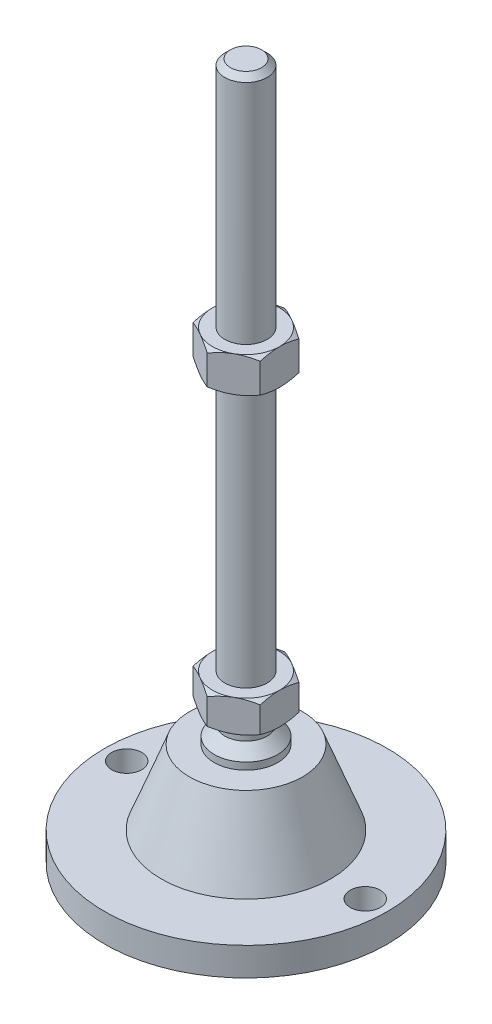
SolidWorks part; units mm, degrees
ref_plane "Спереди" through (0, 0, 0) normal (0, 0, 1) x (1, 0, 0)
ref_plane "Сверху" through (0, 0, 0) normal (0, 1, 0) x (1, 0, 0)
ref_plane "Справа" through (0, 0, 0) normal (1, 0, 0) x (0, 0, -1)
sketch "Эскиз1" plane through (0, 0, 0) normal (0, 0, 1) x (1, 0, 0)
  line L0 (0, 0) -> (-40, 0)
  line L3 (-40, 0) -> (-40, 8)
  line L12 (-6, 47) -> (-6, 195.4)
  line L13 (-6, 195.4) -> (-4.4, 197)
  line L14 (-4.4, 197) -> (0, 197)
  line L15 (0, 197) -> (0, 0) construction
  line L16 (-40, 8) -> (-24, 8)
  line L17 (0, 0) -> (0, 197)
  line L18 (0, 0) -> (0, -7.9595) construction
  line L19 (-6, 47) -> (-6, 38)
  line L21 (-9, 29) -> (-16, 29)
  line L22 (-24, 8) -> (-16, 29)
  line L23 (-9, 29) -> (-9, 31)
  line L24 (-9, 31) -> (-6, 34)
  line L25 (-6, 34) -> (-6, 38)
  line L26 (-6, 47) -> (0, 47) construction
  point P8 (-6, 121.2)
revolve "Повернуть1" add sketch "Эскиз1" angle 360 about L17
ref_plane "Плоскость2" through (0, 38, 0) normal (0, 1, 0) x (1, 0, 0)
sketch "Эскиз2" plane through (0, 38, 0) normal (0, 1, 0) x (1, 0, 0)
  line L1 (0, 10.9697) -> (-9.5, 5.4848)
  line L2 (-9.5, 5.4848) -> (-9.5, -5.4848)
  line L3 (-9.5, -5.4848) -> (0, -10.9697)
  line L4 (0, -10.9697) -> (9.5, -5.4848)
  line L5 (9.5, -5.4848) -> (9.5, 5.4848)
  line L6 (9.5, 5.4848) -> (0, 10.9697)
  circle A0 centre (0, 0) radius 9.5 construction
  dimension "D1" = 19
extrude "Бобышка-Вытянуть1" add sketch "Эскиз2" along normal up to vertex (9 mm away) up to point (-6, 47, 0)
ref_plane "Плоскость1" through (0, 121.2, 0) normal (0, 1, 0) x (1, 0, 0)
sketch "Эскиз3" plane through (0, 121.2, 0) normal (0, 1, 0) x (1, 0, 0)
  line L6 (9.5, 5.4848) -> (0, 10.9697)
  line L7 (0, 10.9697) -> (-9.5, 5.4848)
  line L8 (-9.5, 5.4848) -> (-9.5, -5.4848)
  line L9 (-9.5, -5.4848) -> (0, -10.9697)
  line L10 (0, -10.9697) -> (9.5, -5.4848)
  line L11 (9.5, -5.4848) -> (9.5, 5.4848)
  line L12 (9.5, 5.4848) -> (0, 10.9697)
  line L13 (0, 10.9697) -> (-9.5, 5.4848)
  line L14 (-9.5, 5.4848) -> (-9.5, -5.4848)
  line L15 (-9.5, -5.4848) -> (0, -10.9697)
  line L16 (0, -10.9697) -> (9.5, -5.4848)
  line L17 (9.5, -5.4848) -> (9.5, 5.4848)
  dimension "D1" = 0
extrude "Бобышка-Вытянуть2" add sketch "Эскиз3" along normal blind 10
sketch "Эскиз4" plane through (0, 0, 0) normal (0, 0, 1) x (1, 0, 0)
  line L0 (-9.5, 131.2) -> (-18.1603, 126.2)
  line L1 (-18.1603, 126.2) -> (-18.1603, 131.2)
  line L2 (-18.1603, 131.2) -> (-9.5, 131.2)
  line L3 (-18.1603, 126.2) -> (-9.5, 121.2)
  line L4 (50, 121.2) -> (-50, 121.2) construction
  line L5 (-9.5, 121.2) -> (-18.1603, 121.2)
  line L6 (-18.1603, 121.2) -> (-18.1603, 126.2)
  line L7 (-9.5, 131.2) -> (-9.5, 121.2) construction
  line L8 (-9.5, 47) -> (-17.2942, 47)
  line L9 (-17.2942, 47) -> (-17.2942, 42.5)
  line L10 (-17.2942, 42.5) -> (-9.5, 47)
  line L11 (-9.5, 38) -> (-17.2942, 42.5)
  line L12 (-17.2942, 42.5) -> (-17.2942, 38)
  line L13 (-17.2942, 38) -> (-9.5, 38)
  line L14 (0, 197) -> (0, 96.3793) construction
  line L15 (50, 38) -> (-50, 38) construction
  dimension "D1" = 30
  dimension "D2" = 30
revolve "Вырез-Повернуть2" cut sketch "Эскиз4" angle 360 about L14
sketch "Эскиз5" plane through (0, 8, 0) normal (0, 1, 0) x (1, 0, 0)
  line L0 (33.75, 0) -> (-33.75, 0) construction
  circle A0 centre (-33.75, 0) radius 4.25
  circle A1 centre (33.75, 0) radius 4.25
  circle A2 centre (0, 0) radius 40 construction
  dimension "D1" = 8.5
  dimension "D2" = 2
extrude "Вырез-Вытянуть1" cut sketch "Эскиз5" against normal through all
equation "\"D13@Эскиз1\"=\"D12@Эскиз1\"/2"
